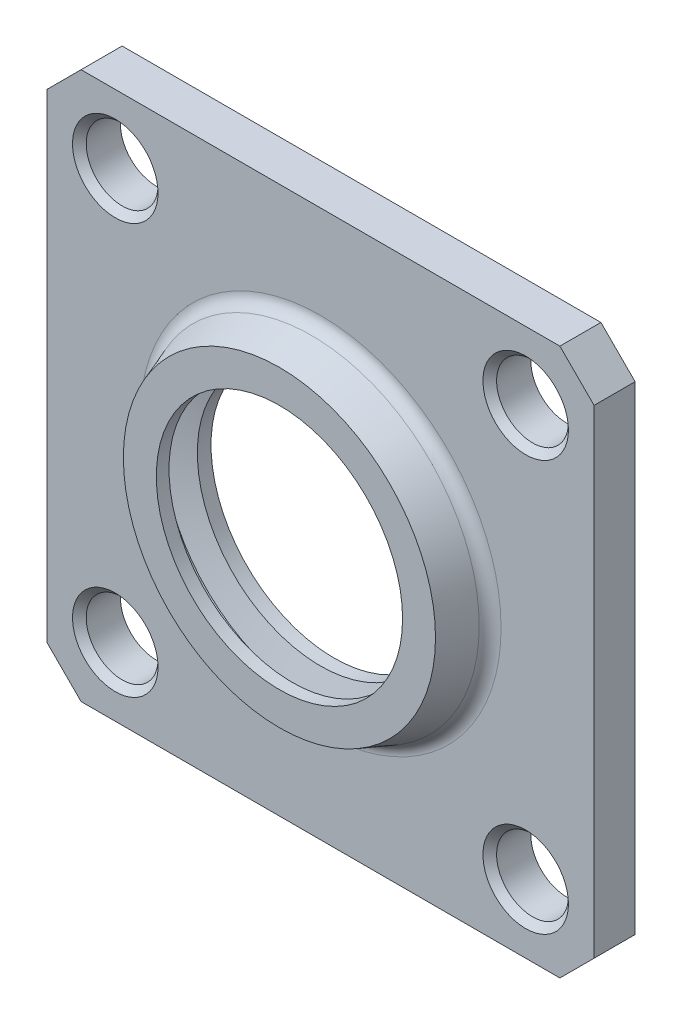
SolidWorks part; units mm, degrees
ref_plane "Front Plane" through (0, 0, 0) normal (0, 0, 1) x (1, 0, 0)
ref_plane "Top Plane" through (0, 0, 0) normal (0, 1, 0) x (1, 0, 0)
ref_plane "Right Plane" through (0, 0, 0) normal (1, 0, 0) x (0, 0, -1)
ref_plane "Plane1" through (0, 0, 6) normal (0, 0, 1) x (1, 0, 0)
sketch "Sketch1" plane through (0, 0, 6) normal (0, 0, 1) x (1, 0, 0)
  line L0 (40, -40) -> (40, 40)
  line L1 (40, 40) -> (-40, 40)
  line L2 (-40, 40) -> (-40, -40)
  line L3 (-40, -40) -> (40, -40)
extrude "Boss-Extrude1" add sketch "Sketch1" against normal blind 6
sketch "Sketch2" plane through (0, 0, 0) normal (0, 1, 0) x (1, 0, 0)
  line L0 (25, -6) -> (0, -6)
  line L1 (0, -6) -> (0, -12)
  line L2 (0, -12) -> (22.8162, -12)
  line L3 (22.8162, -12) -> (25, -6)
  line L4 (0, -6) -> (0, -12) construction
revolve "Revolve1" add sketch "Sketch2" angle 360 about L4
sketch "Sketch3" plane through (0, 0, 0) normal (0, 1, 0) x (1, 0, 0)
  line L0 (26, 0) -> (0, 0)
  line L1 (0, 0) -> (0, -12)
  line L2 (0, -12) -> (18, -12)
  line L3 (18, -12) -> (18, -10.1436)
  line L4 (18, -10.1436) -> (22, -9.0718)
  line L5 (22, -9.0718) -> (22, -7.0718)
  line L6 (22, -7.0718) -> (18, -6)
  line L7 (18, -6) -> (18, -4)
  line L8 (18, -4) -> (26, -4)
  line L9 (26, -4) -> (26, 0)
  line L10 (0, 0) -> (0, -12) construction
revolve "Cut-Revolve1" cut sketch "Sketch3" angle 360 about L10
hole_wizard "Ø10.5 (10.5) Diameter Hole1" positions "Sketch5" profile "Sketch4" hole size "Ø10.5" standard "ANSI Metric"
sketch "Sketch5" plane through (0, 0, 6) normal (0, 0, 1) x (1, 0, 0)
  point P0 (30, 30)
  point P1 (-30, 30)
  point P2 (-30, -30)
  point P3 (30, -30)
sketch "Sketch4" plane through (30, 30, 6) normal (1, 0, 0) x (0, -1, 0)
  line L0 (0, 0) -> (0, 6)
  line L1 (0, 6) -> (5.25, 6)
  line L2 (5.25, 6) -> (5.25, 0)
  line L5 (5.25, 0) -> (0, 0)
  line L11 (0, -6.35) -> (0, 107.95) construction
  dimension "Thru Hole Dia." = 10.5
  dimension "Thru Hole Depth" = 6
chamfer "Chamfer1" distance 5 angle 45 4 edges at (40, -40, 3) (-40, -40, 3) (40, 40, 3) (-40, 40, 3)
chamfer "Chamfer2" distance 1 angle 45 5 edges at (-24.75, -30, 6) (35.25, -30, 6) (26, 0, 0) (-24.75, 30, 6) (35.25, 30, 6)
fillet "Fillet1" radius 1 1 edges at (26, 0, 4)
fillet "Fillet2" radius 2 1 edges at (25, 0, 6)
scale "Scale1" scale about centroid uniform scaling yes scale factor 0.75
